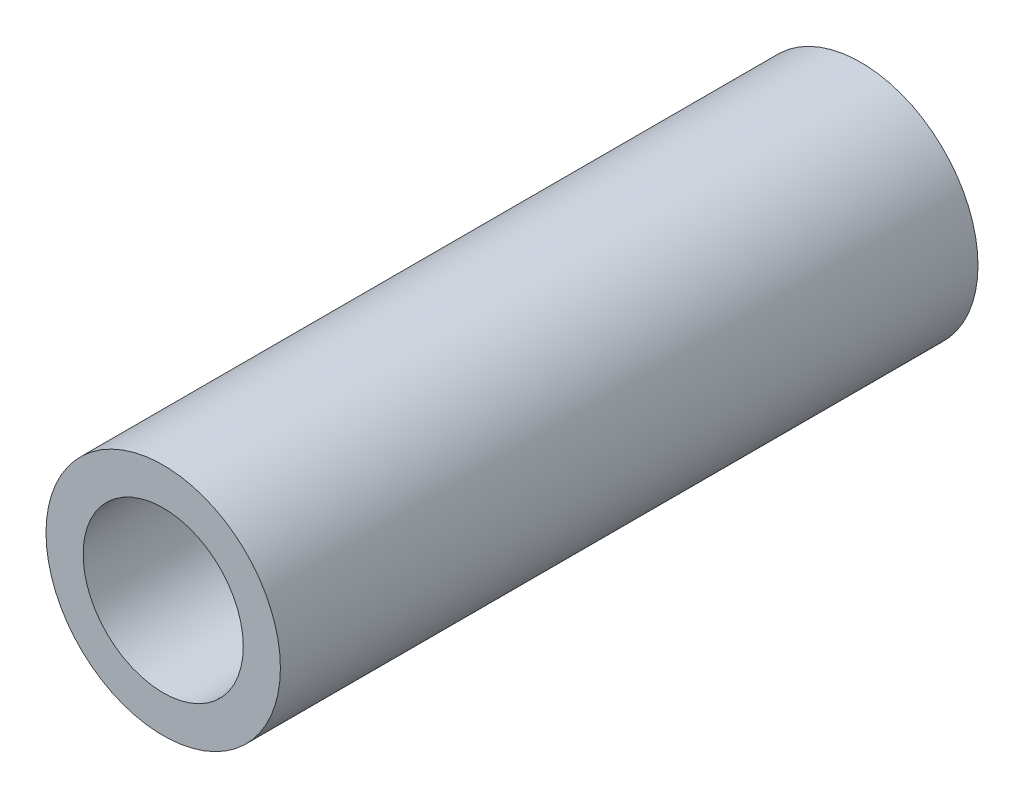
SolidWorks part; units mm, degrees
material "PVC Rigid"
ref_plane "Front" through (0, 0, 0) normal (0, 0, 1) x (1, 0, 0)
ref_plane "Top" through (0, 0, 0) normal (0, 1, 0) x (1, 0, 0)
ref_plane "Right" through (0, 0, 0) normal (1, 0, 0) x (0, 0, -1)
sketch "Sketch1" plane through (0, 0, 0) normal (0, 0, 1) x (1, 0, 0)
  circle A0 centre (0, 0) radius 10.668
  circle A1 centre (0, 0) radius 7.2898
  dimension "D1" = 21.336
  dimension "D2" = 3.3782
extrude "Boss-Extrude1" add sketch "Sketch1" along normal blind 63.5
